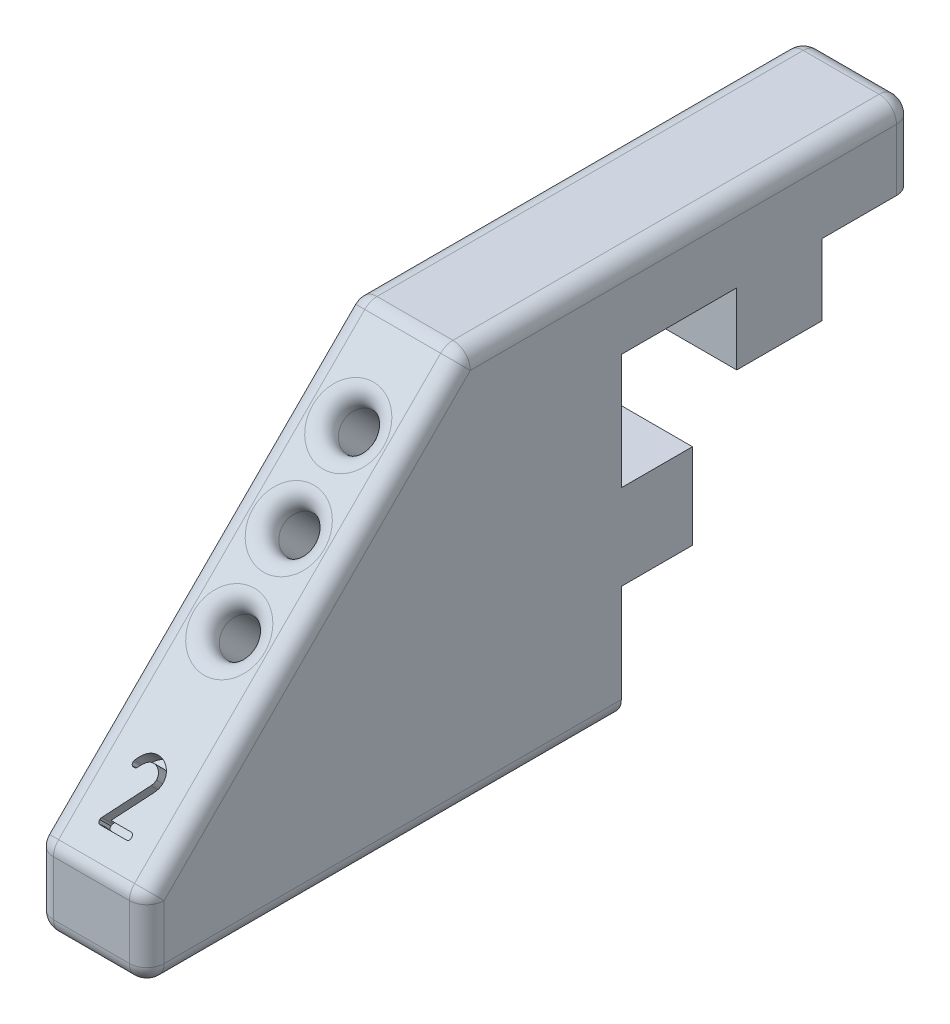
SolidWorks part; units mm, degrees
ref_plane "Спереди" through (0, 0, 0) normal (0, 0, 1) x (1, 0, 0)
ref_plane "Сверху" through (0, 0, 0) normal (0, 1, 0) x (1, 0, 0)
ref_plane "Справа" through (0, 0, 0) normal (1, 0, 0) x (0, 0, -1)
other "Configuration Table"
sketch "Эскиз1" plane through (220, 0, 0) normal (-1, 0, 0) x (0, 0, 1)
  line L2 (-2.7, 10) -> (-2.7, 5.5)
  line L3 (-2.7, 5.5) -> (2.7, 5.5)
  line L4 (2.7, 10) -> (2.7, 5.5)
  line L5 (5.5, 2.7) -> (10, 2.7)
  line L6 (5.5, 2.7) -> (5.5, -2.7)
  line L7 (5.5, -2.7) -> (10, -2.7)
  line L10 (2.7, 10) -> (10, 10)
  line L11 (10, 10) -> (10, 2.7)
  line L12 (-2.7, 10) -> (-8.5, 10)
  line L13 (10, -2.7) -> (10, -10)
  line L14 (10, -10) -> (40, -10)
  line L15 (40, -10) -> (40, -5)
  line L16 (40, -5) -> (20, 15)
  line L17 (3, 10) -> (8.5, 10) construction
  line L18 (-8.5, 10) -> (-8.5, 15)
  line L19 (-8.5, 15) -> (20, 15)
  line L20 (8.5, -10) -> (3, -10) construction
  line L21 (10, 24) -> (10, -24) construction
  line L22 (-3, 10) -> (-3, 8.5) construction
  line L23 (5.25, 8.25) -> (-5.25, 8.25) construction
  line L24 (10, 3) -> (8.5, 3) construction
  point P29 (0, 8.25)
  point P30 (0, 5.5)
  dimension "D1" = 5
  dimension "D2" = 5
  dimension "D3" = 45
  dimension "D4" = 0.3
  dimension "D5" = 4.5
  dimension "D6" = 0.3
  dimension "D7" = 30
extrude "Бобышка-Вытянуть1" add sketch "Эскиз1" along normal blind 7
sketch "Эскиз2" plane through (0, 17.5, 17.5) normal (0, 0.7071, 0.7071) x (1, 0, 0)
  line L0 (213, -3.5355) -> (220, -3.5355) construction
  line L1 (213, -31.8198) -> (220, -31.8198) construction
  circle A0 centre (216.5, -14.1777) radius 1.15
  circle A1 centre (216.5, -14.1777) radius 10.6421 construction
  point P5 (216.5, -3.5355)
  dimension "D1" = 2.3
  dimension "D2" = 7
extrude "Вырез-Вытянуть1" cut sketch "Эскиз2" against normal blind 10
sketch "Эскиз5" plane through (0, 17.5, 17.5) normal (0, 0.7071, 0.7071) x (1, 0, 0)
  line L0 (140, -14.1777) -> (50140, -14.1777) construction
  line L1 (216.5, -14.1777) -> (216.5, -19.4987) construction
  line L2 (216.5, -19.4987) -> (216.5, -24.8198) construction
  circle A0 centre (216.5, -14.1777) radius 10.6421 construction
  circle A1 centre (216.5, -14.1777) radius 10.6421 construction
  circle A2 centre (216.5, -8.8566) radius 1.15
  circle A3 centre (216.5, -19.4987) radius 1.15
  circle A4 centre (216.5, -14.1777) radius 1.15 construction
  dimension "D1" = 10.6421
extrude "Вырез-Вытянуть3" cut sketch "Эскиз5" against normal up to surface (10 mm away) up to face at (216.5, -0.4094, 21.2672)
fillet "Скругление1" radius 1.1 17 edges at (216.5, 15, -8.5) (220, 12.5, -8.5) (213, 12.5, -8.5) (220, -10, 25) (213, -10, 25) (216.5, -10, 40) (220, -7.5, 40) (213, -7.5, 40) (216.5, -5, 40) (216.5, 15, 20) (220, 5, 30) (220, 15, 5.75) (213, 15, 5.75) (213, 5, 30) (216.5, 6.6617, 28.3383) (216.5, 4.5255, 30.4745) (216.5, 10.4243, 24.5757)
sketch "Эскиз3" plane through (0, 17.5, 17.5) normal (0, 0.7071, 0.7071) x (1, 0, 0)
  line L0 (214.1, -29.8642) -> (218.9, -29.8642) construction
  line L1 (214.1, -3.9912) -> (214.1, -31.3642) construction
  line L2 (218.9, -31.3642) -> (218.9, -3.9912) construction
  line L3 (214.1, -31.3642) -> (218.9, -31.3642) construction
  text T0 "1\r\n" font "GOST Common" height 4
  dimension "D1" = 1.5
extrude "Вырез-Вытянуть2" [suppressed] cut sketch "Эскиз3" against normal blind 1
sketch "Эскиз6" plane through (0, 17.5, 17.5) normal (0, 0.7071, 0.7071) x (1, 0, 0)
  line L0 (214.1, -29.8642) -> (218.9, -29.8642) construction
  line L1 (214.1, -29.8642) -> (218.9, -29.8642) construction
  text T0 "2" font "GOST Common" height 4
extrude "Вырез-Вытянуть4" cut sketch "Эскиз6" against normal blind 1
sketch "Эскиз7" [suppressed] plane through (0, 17.5, 17.5) normal (0, 0.7071, 0.7071) x (1, 0, 0)
  line L0 (139.1, -29.8642) -> (148.9, -29.8642) construction
  line L1 (139.1, -29.8642) -> (148.9, -29.8642) construction
  text T0 "3" font "GOST Common" height 4
extrude "Вырез-Вытянуть5" [suppressed] cut sketch "Эскиз7" against normal blind 1
sketch "Эскиз8" [suppressed] plane through (0, 16.3011, 12.7358) normal (0, 0.788, 0.6157) x (1, 0, 0)
  line L0 (135.1, -32.5622) -> (141.9, -32.5622) construction
  line L1 (135.1, -32.5622) -> (141.9, -32.5622) construction
  text T0 "4" font "GOST Common" height 4
extrude "Вырез-Вытянуть6" [suppressed] cut sketch "Эскиз8" against normal blind 1
sketch "Эскиз9" [suppressed] plane through (0, 16.3011, 12.7358) normal (0, 0.788, 0.6157) x (1, 0, 0)
  line L0 (134.1, -32.5622) -> (141.9, -32.5622) construction
  line L1 (134.1, -32.5622) -> (141.9, -32.5622) construction
  text T0 "5" font "GOST Common" height 4
extrude "Вырез-Вытянуть7" [suppressed] cut sketch "Эскиз9" against normal blind 1
sketch "Эскиз10" [suppressed] plane through (0, 16.3011, 12.7358) normal (0, 0.788, 0.6157) x (1, 0, 0)
  line L0 (133.1, -32.5622) -> (141.9, -32.5622) construction
  line L1 (133.1, -32.5622) -> (141.9, -32.5622) construction
  text T0 "6" font "GOST Common" height 4
extrude "Вырез-Вытянуть8" [suppressed] cut sketch "Эскиз10" against normal blind 1
sketch "Эскиз11" [suppressed] plane through (0, 16.3011, 12.7358) normal (0, 0.788, 0.6157) x (1, 0, 0)
  line L0 (132.1, -32.5622) -> (141.9, -32.5622) construction
  line L1 (132.1, -32.5622) -> (141.9, -32.5622) construction
  text T0 "7" font "GOST Common" height 4
extrude "Вырез-Вытянуть9" [suppressed] cut sketch "Эскиз11" against normal blind 1
sketch "Эскиз12" [suppressed] plane through (0, 16.3011, 12.7358) normal (0, 0.788, 0.6157) x (1, 0, 0)
  line L0 (131.1, -32.5622) -> (141.9, -32.5622) construction
  line L1 (131.1, -32.5622) -> (141.9, -32.5622) construction
  text T0 "8" font "GOST Common" height 4
extrude "Вырез-Вытянуть10" [suppressed] cut sketch "Эскиз12" against normal blind 1
sketch "Эскиз13" [suppressed] plane through (0, 16.3011, 12.7358) normal (0, 0.788, 0.6157) x (1, 0, 0)
  line L0 (130.1, -32.5622) -> (141.9, -32.5622) construction
  line L1 (130.1, -32.5622) -> (141.9, -32.5622) construction
  text T0 "9" font "GOST Common" height 4
extrude "Вырез-Вытянуть11" [suppressed] cut sketch "Эскиз13" against normal blind 1
sketch "Эскиз14" [suppressed] plane through (0, 16.3011, 12.7358) normal (0, 0.788, 0.6157) x (1, 0, 0)
  line L0 (129.1, -32.5622) -> (141.9, -32.5622) construction
  line L1 (129.1, -32.5622) -> (141.9, -32.5622) construction
  text T0 "10" font "GOST Common" height 4
extrude "Вырез-Вытянуть12" [suppressed] cut sketch "Эскиз14" against normal blind 1
sketch "Эскиз15" [suppressed] plane through (0, 16.3011, 12.7358) normal (0, 0.788, 0.6157) x (1, 0, 0)
  line L0 (128.1, -32.5622) -> (141.9, -32.5622) construction
  line L1 (128.1, -32.5622) -> (141.9, -32.5622) construction
  text T0 "11" font "GOST Common" height 4
extrude "Вырез-Вытянуть13" [suppressed] cut sketch "Эскиз15" against normal blind 1
sketch "Эскиз16" [suppressed] plane through (0, 16.3011, 12.7358) normal (0, 0.788, 0.6157) x (1, 0, 0)
  line L0 (127.1, -32.5622) -> (141.9, -32.5622) construction
  line L1 (127.1, -32.5622) -> (141.9, -32.5622) construction
  text T0 "12" font "GOST Common" height 4
extrude "Вырез-Вытянуть14" [suppressed] cut sketch "Эскиз16" against normal blind 1
sketch "Эскиз17" [suppressed] plane through (0, 16.3011, 12.7358) normal (0, 0.788, 0.6157) x (1, 0, 0)
  line L0 (126.1, -32.5622) -> (141.9, -32.5622) construction
  line L1 (126.1, -32.5622) -> (141.9, -32.5622) construction
  text T0 "13" font "GOST Common" height 4
extrude "Вырез-Вытянуть15" [suppressed] cut sketch "Эскиз17" against normal blind 1
sketch "Эскиз18" [suppressed] plane through (0, 16.3011, 12.7358) normal (0, 0.788, 0.6157) x (1, 0, 0)
  line L0 (125.1, -32.5622) -> (141.9, -32.5622) construction
  line L1 (125.1, -32.5622) -> (141.9, -32.5622) construction
  text T0 "14" font "GOST Common" height 4
extrude "Вырез-Вытянуть16" [suppressed] cut sketch "Эскиз18" against normal blind 1
sketch "Эскиз19" [suppressed] plane through (0, 16.3011, 12.7358) normal (0, 0.788, 0.6157) x (1, 0, 0)
  line L0 (124.1, -32.5622) -> (141.9, -32.5622) construction
  line L1 (124.1, -32.5622) -> (141.9, -32.5622) construction
  text T0 "15" font "GOST Common" height 4
extrude "Вырез-Вытянуть17" [suppressed] cut sketch "Эскиз19" against normal blind 1
sketch "Эскиз20" [suppressed] plane through (0, 17.5, 17.5) normal (0, 0.7071, 0.7071) x (1, 0, 0)
  line L0 (139.1, -29.8642) -> (148.9, -29.8642) construction
  line L1 (139.1, -29.8642) -> (148.9, -29.8642) construction
  text T0 "16" font "GOST Common" height 4
extrude "Вырез-Вытянуть18" [suppressed] cut sketch "Эскиз20" against normal blind 1
sketch "Эскиз21" [suppressed] plane through (0, 17.5, 17.5) normal (0, 0.7071, 0.7071) x (1, 0, 0)
  line L0 (148.9, -3.9912) -> (139.1, -3.9912) construction
  line L1 (144, -10.2517) -> (140.6, -12.2147)
  line L2 (140.6, -12.2147) -> (140.6, -16.1407)
  line L3 (140.6, -16.1407) -> (144, -18.1037)
  line L4 (144, -18.1037) -> (147.4, -16.1407)
  line L5 (147.4, -16.1407) -> (147.4, -12.2147)
  line L6 (147.4, -12.2147) -> (144, -10.2517)
  circle A0 centre (144, -14.1777) radius 3.4 construction
  circle A2 centre (144, -14.1777) radius 1.65
  circle A3 centre (144, -14.1777) radius 1.65 construction
  point P10 (144, -3.9912)
  dimension "D1" = 6.8
  dimension "D2" = 0
extrude "Вырез-Вытянуть19" [suppressed] cut sketch "Эскиз21" against normal blind 10
fillet "Скругление2" [suppressed] radius 1
